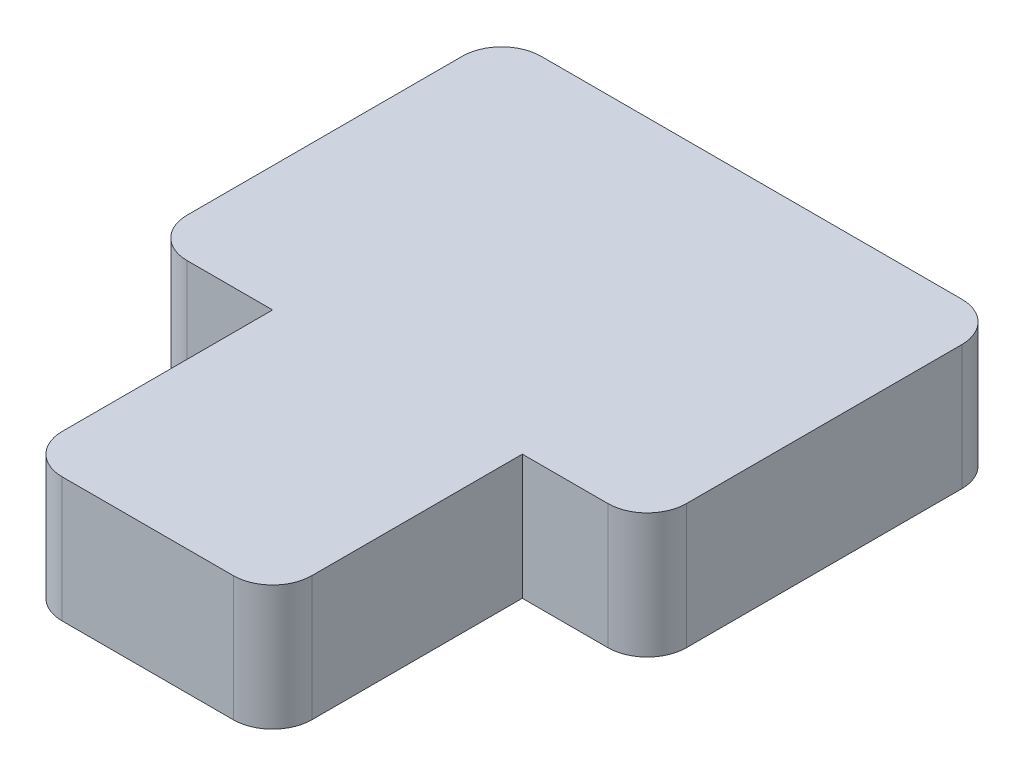
SolidWorks part; units mm, degrees
material "Beech"
ref_plane "Front Plane" through (0, 0, 0) normal (0, 0, 1) x (1, 0, 0)
ref_plane "Top Plane" through (0, 0, 0) normal (0, 1, 0) x (1, 0, 0)
ref_plane "Right Plane" through (0, 0, 0) normal (1, 0, 0) x (0, 0, -1)
sketch "Sketch1" plane through (0, 0, 0) normal (0, 1, 0) x (1, 0, 0)
  line L0 (0, 0) -> (6.35, 0)
  line L1 (0, 0) -> (0, 6.35)
  line L2 (6.35, 0) -> (6.35, 6.35)
  line L4 (-3.175, 15.35) -> (-3.175, 6.35)
  line L5 (-3.175, 15.35) -> (9.525, 15.35)
  line L6 (-3.175, 6.35) -> (0, 6.35)
  line L7 (9.525, 15.35) -> (9.525, 6.35)
  line L8 (6.35, 6.35) -> (9.525, 6.35)
  dimension "D1" = 6.35
  dimension "D2" = 6.35
  dimension "D3" = 12.7
  dimension "D4" = 9
extrude "MotorSupport_Extrude" add sketch "Sketch1" along normal blind 3.175
fillet "MotorSupport_BottomFillet" radius 1 6 edges at (0, 1.5875, 0) (6.35, 1.5875, 0) (-3.175, 1.5875, -15.35) (-3.175, 1.5875, -6.35) (9.525, 1.5875, -6.35) (9.525, 1.5875, -15.35)
equation "\"CageLeftBottomEdge\"=22.11mm"
equation "\"CageLeftTopEdge\"=22.11mm"
equation "\"CageRightBottomEdge\"=21.63mm"
equation "\"CageRightTopEdge\"=21.63mm"
equation "\"CageHeight\"=86.04mm"
equation "\"CageLength\"=73.76mm"
equation "\"CageTopScrewClearance\"=10mm"
equation "\"CageBottomScrewClearance\"=25mm"
equation "\"CageLeftTopDepth\"= 11.65mm"
equation "\"CageLeftBottomDepth\"=11.11mm"
equation "\"CageLeftTopHeight\"=8.56175mm"
equation "\"CageLeftBottomHeight\"=16mm"
equation "\"CageRightTopDepth\"= 11.05mm"
equation "\"CageRightBottomDepth\"=10.58mm"
equation "\"CageRightTopHeight\"=9.6mm"
equation "\"CageRightBottomHeight\"=15.49mm"
equation "\"CageLeftTopChannelDepth\"=2.41908mm"
equation "\"CageLeftBottomChannelDepth\"=2.588mm"
equation "\"CageLeftChannelHeight\"=11.7mm"
equation "\"CageRightTopChannelDepth\"=2.32mm"
equation "\"CageRightBottomChannelDepth\"=2.318mm"
equation "\"CageRightChannelHeight\"=10mm"
equation "\"CageChanRelHeight\"=23.99mm"
equation "\"CageChanRelDepth\"=5.492mm"
equation "\"CageChamberRadius\"=16.261mm"
equation "\"CageScrewDiameter\"=4.8mm"
equation "\"CageSetScrewDiameter\"=3.5mm"
equation "\"CageAxleRadius\"=6.639mm"
equation "\"CageAxleKeyHeight\"=1.619mm"
equation "\"CageAxleKeyWidth\"=2.662mm"
equation "\"CageHoseWindowWidth\"=16.29mm"
equation "\"CageHoseWindowHeight\"=26.5mm"
equation "\"CageHoseWindow-Edge\"=8.89mm"
equation "\"CageScrew-VerticalEdge\"=5.0mm"
equation "\"CageScrew-HorizontalEdge\"=7.5mm"
equation "\"CageScrew-HoseCornerScrewEdge\"=4.45mm"
equation "\"CageAxle-BottomEdge\"=56.05mm"
equation "\"CageAxle-FrontEdge\"=46.03mm"
equation "\"CageBackSetScrew-Axle\"=40mm"
equation "\"CageFrontSetScrew-Axle\"=22mm"
equation "\"CageVelocityWindow-BackEdge\"=34.8mm"
equation "\"CageVelocityWindow-BottomEdge\"=27.55mm"
equation "\"CageVelocityWindowHeight\"=22.29mm"
equation "\"CageVelocityWindowWidth\"=12.61mm"
equation "\"TriggerSlot-BottomEdge\"=6.35mm"
equation "\"TriggerSlot-FrontEdge\"=15mm"
equation "\"TriggerSlotSize\"=6.7mm"
equation "\"TriggerRackOffset\"=6mm"
equation "\"TriggerSlotSizeInt\"=.25in"
equation "\"MotorMountLegLength\"=.25in"
equation "\"GearOffset\"=.264907in"
equation "\"TriggerSlotSpacing\"=.25in"
equation "\"D1@Sketch1\"=\"TriggerSlotSizeInt\""
equation "\"D2@Sketch1\"=\"MotorMountLegLength\""
equation "\"D3@Sketch1\"=2*\"TriggerSlotSizeInt\""
equation "\"D4@Sketch1\"=1.5*\"TriggerRackOffset\""
equation "\"D1@MotorSupport_Extrude\"=.125in"
equation "\"TriggerMiniSlotWidth\"=3.5mm"
equation "\"TriggerRackWidth\"=6.5mm"
equation "\"pandiscradius\"=14in"
equation "\"towermaterialwidth\"=.25in"
equation "\"towerslotlength\"=.5in"
equation "\"towermarkerspace\"=5in"
equation "\"towerslothorizoffset\"=1in"
equation "\"towerslothorizspacing\"=2in"
equation "\"towerslotvertoffset\"=3in"
equation "\"towerslotvertspacing\"=1in"
equation "\"towerheight\"=12in"
equation "\"towerupslot\"=1in"
equation "\"toweraxle\"=.5in"
equation "\"stepperouterrad\"=10mm"
equation "\"stepperscrewsize\"=3.45mm"
equation "\"stepperscrewc2c\"=49.5mm"
equation "\"stepperdepthoffset\"=24mm"
equation "\"stepperhorizoffset\"=22.91mm"
equation "\"shaftslotOD\"=18.8mm"
equation "\"shaftslotID\"=13.28mm"
equation "\"shaftkeywidth\"=2.67mm"
equation "\"shaftkeydepth\"=1.8mm"
equation "\"shaftcollartotaldepth\"=9.71mm"
equation "\"shaftsquaredepth\"=6mm"
equation "\"shaftsetscrewsize\"=3.5mm"
equation "\"shaftkeytightdepth\"=1.85mm"
equation "\"shaftslottightID\"=12.78mm"
equation "\"shaftsetscrewoffset\"=9mm"
equation "\"cagecollartotaldepth\"=20mm"
equation "\"cagecollartotalwidth\"=35mm"
equation "\"cagecollarbasedepth\"=4mm"
equation "\"gearhubintdiam\"=30mm"
equation "\"gearhubintwid\"=12.21mm"
equation "\"towerspeedwidth\"=2in"
equation "\"towerspeedheight\"=8in"
equation "\"towerspeedgap\"=2in"
equation "\"stepperaxleflat\"=.037in"
equation "\"stepperaxlerad\"=0.11811024in"
equation "\"ajaxaxlesize\"=3.87mm"
equation "\"ajaxinnercut\"=2.3mm"
equation "\"ajaxwidth\"=6.1mm"
equation "\"ajaxdiametral\"=25.8854"
equation "\"ajaxcutoutdepth\"=2.3mm"
equation "\"ajax4020gap\"=29.5mm"
equation "\"ajax4010gap\"=24.5mm"
equation "\"ajax20hubbuffer\"=6.1mm"
equation "\"ajax20hubholeoffset\"=.19685in"
equation "\"ajax20hubholesize\"=.059055in"
equation "\"ajax20cutoutint\"=13.4mm"
equation "\"ajax40hubholesize\"=7.21mm"
equation "\"ajax40hubholeoffset\"=10mm"
equation "\"ajax40hubbuffer\"=8.9mm"
equation "\"ajax40cutoutint\"=32.6mm"
equation "\"bearingpandiscrad\"=6.8in"
equation "\"bearingpandiscang\"=48.75deg"
equation "\"bearingclearholedist\"=4.7345in"
equation "\"bearingclearholesize\"=.5in"
equation "\"bearingclearholeang\"=22.5deg"
equation "\"bearingmountholedist\"=4.25in"
equation "\"bearingwirehole\"=1.5in"
equation "\"no6diam\"=.146in"
equation "\"shortconangle\"=20deg"
equation "\"shortconlen\"=.875in"
equation "\"longconlen\"=1.25in"
equation "\"longconangle\"=15deg"
